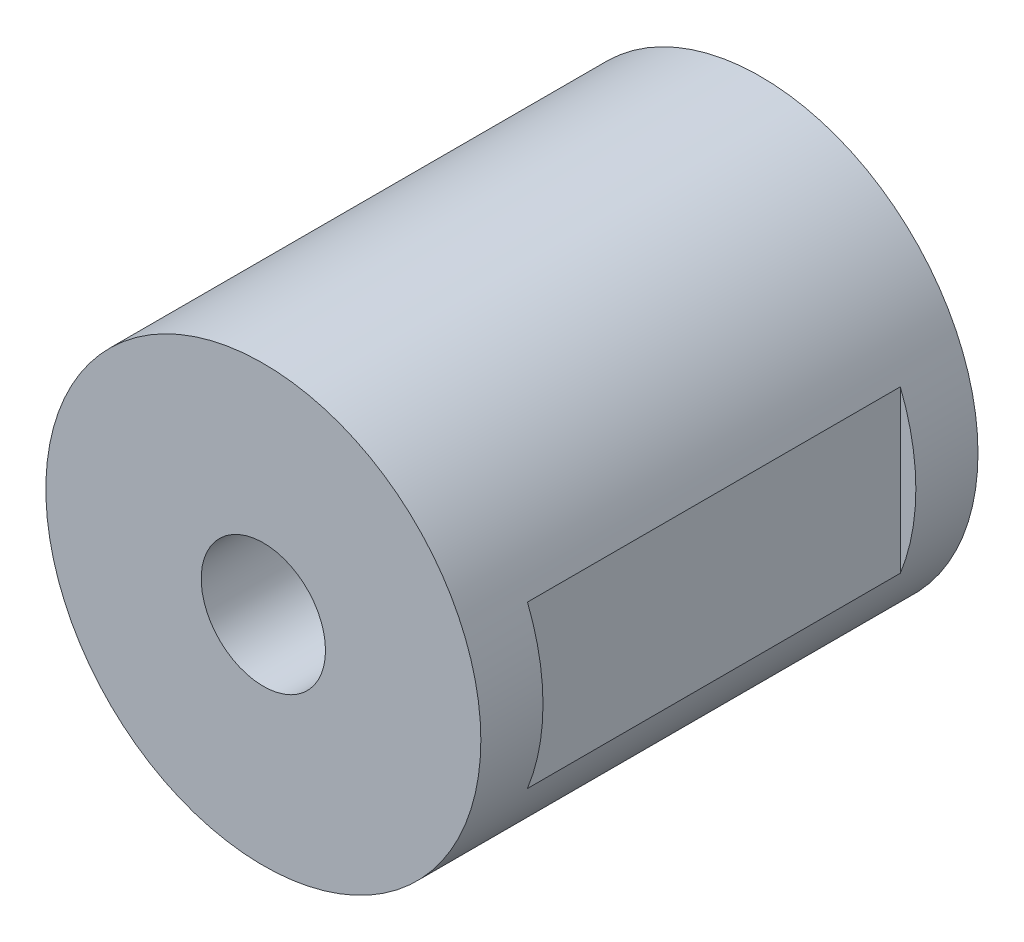
SolidWorks part; units mm, degrees
ref_plane "Front Plane" through (0, 0, 0) normal (0, 0, 1) x (1, 0, 0)
ref_plane "Top Plane" through (0, 0, 0) normal (0, 1, 0) x (1, 0, 0)
ref_plane "Right Plane" through (0, 0, 0) normal (1, 0, 0) x (0, 0, -1)
sketch "Sketch1" plane through (0, 0, 0) normal (0, 0, 1) x (1, 0, 0)
  circle A0 centre (0, 0) radius 35
  dimension "D1" = 70
extrude "Boss-Extrude1" add sketch "Sketch1" along normal blind 80
sketch "Sketch2" plane through (0, 0, 80) normal (0, 0, 1) x (1, 0, 0)
  circle A0 centre (0, 0) radius 10
  dimension "D1" = 20
extrude "Cut-Extrude1" cut sketch "Sketch2" against normal through all
ref_plane "Plane1" through (35, 0, 0) normal (1, 0, 0) x (0, 0, -1)
sketch "Sketch3" plane through (35, 0, 0) normal (1, 0, 0) x (0, 0, -1)
  line L0 (0, -35) -> (0, 35) construction
  line L1 (-70, 12.99) -> (-10, 12.99)
  line L2 (-70, 12.99) -> (-70, -12.99)
  line L3 (-70, -12.99) -> (-10, -12.99)
  line L4 (-10, 12.99) -> (-10, -12.99)
  line L5 (-70, 12.99) -> (-10, -12.99) construction
  line L6 (-70, -12.99) -> (-10, 12.99) construction
  line L7 (-80, -35) -> (0, -35) construction
  point P0 (-40, 0)
  dimension "D1" = 60
  dimension "D2" = 25.98
  dimension "D3" = 10
  dimension "D4" = 22.01
extrude "Cut-Extrude5" cut sketch "Sketch3" against normal blind 2.5
ref_plane "Plane2" through (0, -35, 0) normal (0, -1, 0) x (-1, 0, 0)
sketch "Sketch4" plane through (0, -35, 0) normal (0, -1, 0) x (-1, 0, 0)
  line L0 (35, 0) -> (-35, 0) construction
  line L1 (-18.03, -20) -> (18.03, -20)
  line L2 (-18.03, -20) -> (-18.03, -60)
  line L3 (-18.03, -60) -> (18.03, -60)
  line L4 (18.03, -20) -> (18.03, -60)
  line L5 (-18.03, -20) -> (18.03, -60) construction
  line L6 (-18.03, -60) -> (18.03, -20) construction
  line L7 (35, -80) -> (35, 0) construction
  point P0 (0, -40)
  dimension "D1" = 36.06
  dimension "D2" = 40
  dimension "D3" = 20
  dimension "D4" = 16.97
extrude "Cut-Extrude6" cut sketch "Sketch4" against normal blind 5
